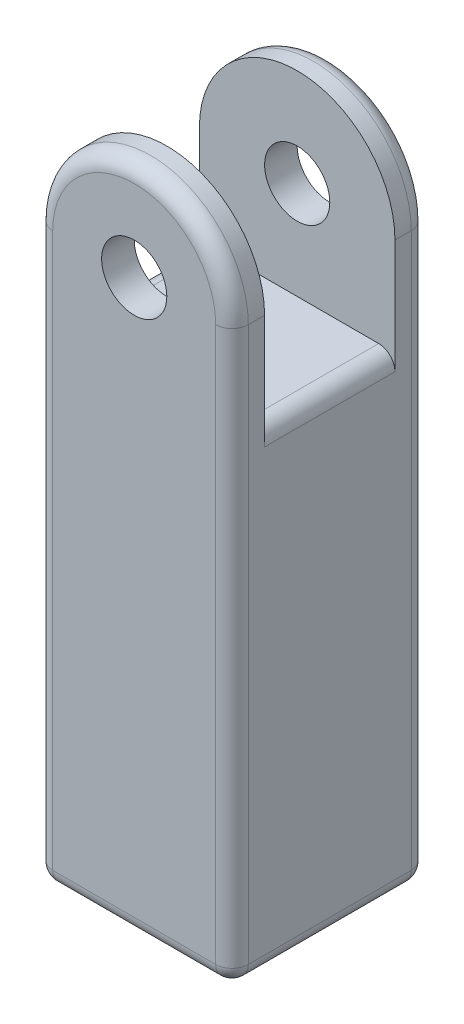
SolidWorks part; units mm, degrees
ref_plane "前基準面" through (0, 0, 0) normal (0, 0, 1) x (1, 0, 0)
ref_plane "上基準面" through (0, 0, 0) normal (0, 1, 0) x (1, 0, 0)
ref_plane "右基準面" through (0, 0, 0) normal (1, 0, 0) x (0, 0, -1)
sketch "草圖1" plane through (0, 0, 0) normal (0, 1, 0) x (1, 0, 0)
  line L1 (-30, 30) -> (30, 30)
  line L2 (-30, 30) -> (-30, -30)
  line L3 (-30, -30) -> (30, -30)
  line L4 (30, 30) -> (30, -30)
  line L5 (-30, 30) -> (30, -30) construction
  line L6 (-30, -30) -> (30, 30) construction
  point P0 (0, 0)
  dimension "D1" = 60
  dimension "D2" = 60
extrude "填料-伸長1" add sketch "草圖1" along normal blind 150
sketch "草圖2" plane through (0, 0, 0) normal (0, -1, 0) x (1, 0, 0)
  circle A0 centre (0, 0) radius 15
  dimension "D1" = 30
extrude "除料-伸長1" cut sketch "草圖2" against normal blind 30
sketch "草圖3" plane through (0, 0, 30) normal (0, 0, 1) x (1, 0, 0)
  line L0 (0, 150) -> (0, 193.1328) construction
  line L1 (-30, 150) -> (30, 150) construction
  line L2 (-30, 150) -> (-30, 175)
  line L3 (-30, 150) -> (30, 150)
  line L4 (30, 150) -> (30, 175)
  arc A0 (30, 175) -> (-30, 175) centre (0, 175) ccw
  circle A1 centre (0, 175) radius 10
  dimension "D1" = 20
  dimension "D2" = 25
extrude "填料-伸長2" add sketch "草圖3" against normal up to surface (60 mm away) up to face at (0, 75, -30)
sketch "草圖4" plane through (-30, 0, 0) normal (-1, 0, 0) x (0, 0, 1)
  line L0 (30, 205) -> (-30, 205) construction
  line L1 (-20, 205) -> (20, 205)
  line L2 (-20, 205) -> (-20, 145)
  line L3 (-20, 145) -> (20, 145)
  line L4 (20, 205) -> (20, 145)
  line L5 (0, 206.1582) -> (0, 123.5677) construction
  dimension "D1" = 60
  dimension "D2" = 40
extrude "除料-伸長2" cut sketch "草圖4" against normal through all
fillet "圓角1" radius 5 12 edges at (30, 87.5, -30) (0, 205, 30) (0, 205, -30) (-30, 87.5, -30) (0, 0, -30) (-30, 87.5, 30) (30, 87.5, 30) (0, 0, 30) (30, 145, 0) (-30, 145, 0) (30, 0, 0) (-30, 0, 0)
